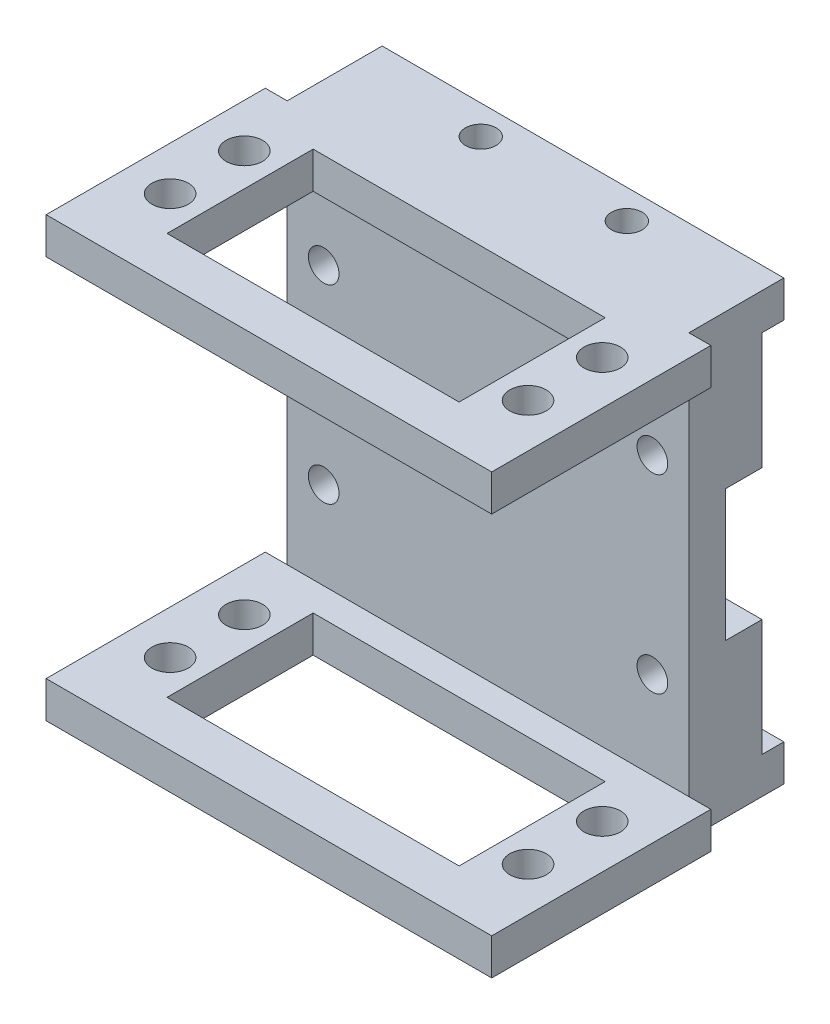
SolidWorks part; units mm, degrees
ref_plane "Front Plane" through (0, 0, 0) normal (0, 0, 1) x (1, 0, 0)
ref_plane "Top Plane" through (0, 0, 0) normal (0, 1, 0) x (1, 0, 0)
ref_plane "Right Plane" through (0, 0, 0) normal (1, 0, 0) x (0, 0, -1)
sketch "Sketch1" plane through (0, 0, 0) normal (0, 0, 1) x (1, 0, 0)
  line L0 (23.841, 9.1341) -> (28.841, 9.1341)
  line L1 (19.841, 25.1341) -> (19.841, 13.1341)
  line L2 (-26.159, 9.1341) -> (-21.159, 9.1341)
  line L3 (-17.159, 13.1341) -> (-17.159, 25.1341)
  line L4 (28.841, -8.8659) -> (23.841, -8.8659)
  line L5 (19.841, -12.8659) -> (19.841, -24.8659)
  line L6 (-17.159, -24.8659) -> (-17.159, -12.8659)
  line L7 (-21.159, -8.8659) -> (-26.159, -8.8659)
  line L8 (-17.159, -24.8659) -> (-26.159, -24.8659)
  line L9 (-26.159, -8.8659) -> (-26.159, -24.8659)
  line L10 (28.841, -24.8659) -> (28.841, -8.8659)
  line L11 (28.841, -24.8659) -> (19.841, -24.8659)
  line L12 (28.841, 9.1341) -> (28.841, 25.1341)
  line L13 (19.841, 25.1341) -> (28.841, 25.1341)
  line L14 (-26.159, 25.1341) -> (-17.159, 25.1341)
  line L15 (-26.159, 25.1341) -> (-26.159, 9.1341)
  arc A0 (19.841, 13.1341) -> (23.841, 9.1341) centre (23.841, 13.1341) ccw
  arc A1 (-21.159, 9.1341) -> (-17.159, 13.1341) centre (-21.159, 13.1341) ccw
  arc A2 (23.841, -8.8659) -> (19.841, -12.8659) centre (23.841, -12.8659) ccw
  arc A3 (-17.159, -12.8659) -> (-21.159, -8.8659) centre (-21.159, -12.8659) ccw
extrude "Boss-Extrude1" add sketch "Sketch1" along normal blind 5
sketch "Sketch2" plane through (0, 0, 5) normal (0, 0, 1) x (1, 0, 0)
  line L1 (-26.159, 25.1341) -> (28.841, 25.1341)
  line L2 (-26.159, 25.1341) -> (-26.159, -24.8659)
  line L3 (-26.159, -24.8659) -> (28.841, -24.8659)
  line L4 (28.841, 25.1341) -> (28.841, -24.8659)
  line L5 (-26.159, 25.1341) -> (28.841, -24.8659) construction
  line L6 (-26.159, -24.8659) -> (28.841, 25.1341) construction
  point P4 (1.341, 0.1341)
extrude "Boss-Extrude2" add sketch "Sketch2" along normal blind 5
sketch "Sketch3" plane through (0, 25.1341, 0) normal (0, 1, 0) x (1, 0, 0)
  line L0 (28.841, 0) -> (28.841, 12) construction
  line L1 (-26.159, -10) -> (28.841, -10)
  line L2 (-26.159, -10) -> (-26.159, 3)
  line L3 (-26.159, 3) -> (28.841, 3)
  line L4 (28.841, -10) -> (28.841, 3)
  line L5 (-26.159, -10) -> (28.841, 3) construction
  line L6 (-26.159, 3) -> (28.841, -10) construction
  line L7 (-5.159, 3) -> (-12.159, 3) construction
  circle A0 centre (-8.659, -1) radius 2.1
  circle A1 centre (11.341, -1) radius 2.1
  point P4 (1.341, -3.5)
extrude "Boss-Extrude3" add sketch "Sketch3" along normal blind 5
ref_plane "Plane1" through (0, 0.1341, 0) normal (0, -1, 0) x (-1, 0, 0)
mirror "Mirror1" about plane through (0, 0.1341, 0) normal (0, -1, 0) of "Boss-Extrude3"
sketch "Sketch4" plane through (0, 30.1341, 0) normal (0, 1, 0) x (1, 0, 0)
  line L0 (-26.159, 3) -> (-26.159, -10) construction
  line L1 (-29.159, -10) -> (31.841, -10)
  line L2 (-29.159, -10) -> (-29.159, -40)
  line L3 (-29.159, -40) -> (31.841, -40)
  line L4 (31.841, -10) -> (31.841, -40)
  line L5 (-29.159, -10) -> (31.841, -40) construction
  line L6 (-29.159, -40) -> (31.841, -10) construction
  line L7 (28.841, -10) -> (28.841, 3) construction
  point P4 (1.341, -25)
  point P6 (0, 0)
  point P7 (0, 0)
  dimension "D1" = 30
  dimension "D2" = 3
  dimension "D3" = 3
extrude "Boss-Extrude4" add sketch "Sketch4" against normal blind 5
mirror "Mirror2" about plane through (0, 0.1341, 0) normal (0, -1, 0) of "Boss-Extrude4"
sketch "Sketch5" plane through (0, 25.1341, 0) normal (0, -1, 0) x (1, 0, 0)
  line L0 (-24.709, 33.9459) -> (-17.659, 33.9459) construction
  line L1 (-18.659, 33.9459) -> (21.3242, 33.9459)
  line L2 (-18.659, 33.9459) -> (-18.659, 13.9459)
  line L3 (-18.659, 13.9459) -> (21.3242, 13.9459)
  line L4 (21.3242, 33.9459) -> (21.3242, 13.9459)
  line L5 (-18.659, 33.9459) -> (21.3242, 13.9459) construction
  line L6 (-18.659, 13.9459) -> (21.3242, 33.9459) construction
  line L7 (27.391, 13.9459) -> (20.341, 13.9459) construction
  circle A0 centre (-23.159, 29.0259) radius 2.5
  circle A1 centre (-23.159, 18.8659) radius 2.5
  circle A2 centre (25.841, 29.0259) radius 2.5
  circle A3 centre (25.841, 18.8659) radius 2.5
  point P16 (1.3326, 23.9459)
extrude "Cut-Extrude3" cut sketch "Sketch5" against normal blind 5
sketch "Sketch7" plane through (0, 0, 10) normal (0, 0, 1) x (1, 0, 0)
  circle A0 centre (23.841, -12.8659) radius 2.1
  circle A1 centre (-21.159, -12.8659) radius 2.1
  circle A2 centre (23.841, 13.1341) radius 2.1
  circle A3 centre (-21.159, 13.1341) radius 2.1
extrude "Cut-Extrude4" cut sketch "Sketch7" against normal through all
mirror "Mirror3" about plane through (0, 0.1341, 0) normal (0, -1, 0) of "Cut-Extrude3"
